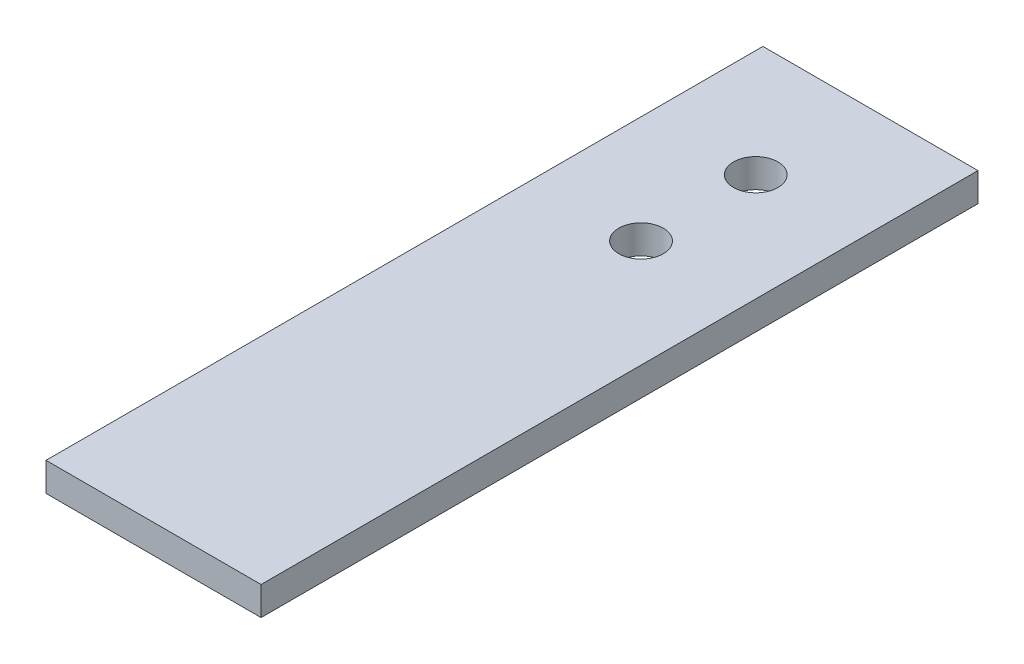
SolidWorks part; units mm, degrees
ref_plane "前视基准面" through (0, 0, 0) normal (0, 0, 1) x (1, 0, 0)
ref_plane "上视基准面" through (0, 0, 0) normal (0, 1, 0) x (1, 0, 0)
ref_plane "右视基准面" through (0, 0, 0) normal (1, 0, 0) x (0, 0, -1)
sketch "草图1" plane through (0, 0, 0) normal (0, 1, 0) x (1, 0, 0)
  line L0 (0, 0) -> (0, 50)
  line L1 (0, 50) -> (15, 50)
  line L2 (15, 50) -> (15, 0)
  line L3 (15, 0) -> (0, 0)
  line L4 (7.5, 38) -> (7.5, 34)
  line L5 (7.5, 42) -> (7.5, 38)
  circle A0 centre (7.5, 42) radius 1.55
  circle A1 centre (7.5, 34) radius 1.55
extrude "凸台-拉伸1" add sketch "草图1" along normal blind 2
